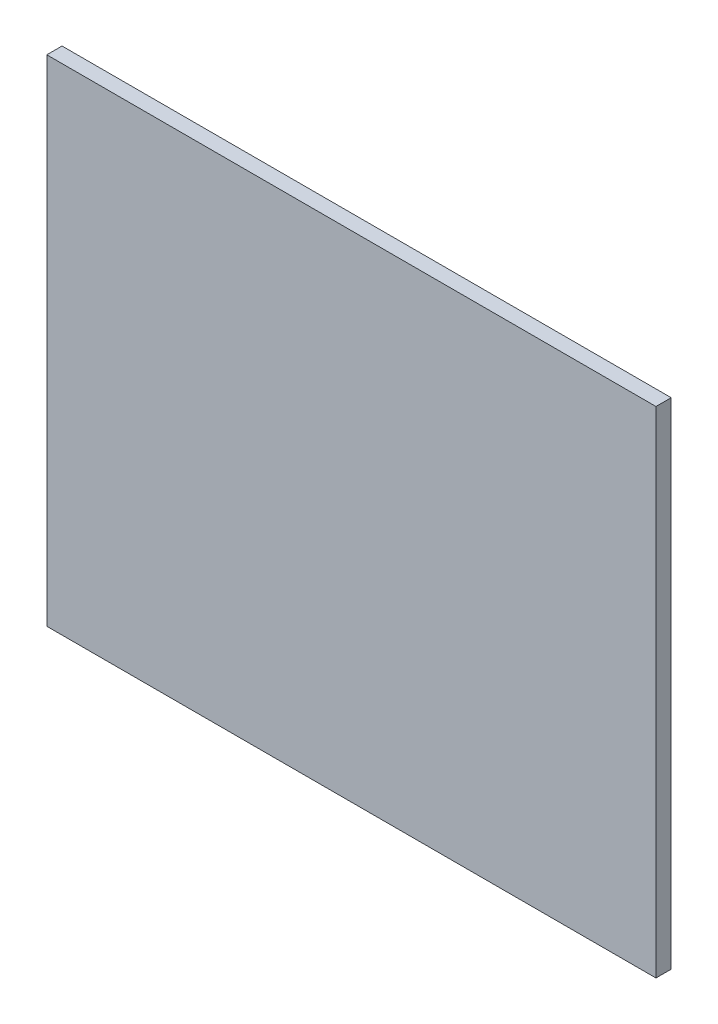
SolidWorks part; units mm, degrees
ref_plane "前视基准面" through (0, 0, 0) normal (0, 0, 1) x (1, 0, 0)
ref_plane "上视基准面" through (0, 0, 0) normal (0, 1, 0) x (1, 0, 0)
ref_plane "右视基准面" through (0, 0, 0) normal (1, 0, 0) x (0, 0, -1)
sketch "草图1" plane through (0, 0, 0) normal (0, 0, 1) x (1, 0, 0)
  line L1 (-400, -325) -> (400, -325)
  line L2 (-400, -325) -> (-400, 325)
  line L3 (-400, 325) -> (400, 325)
  line L4 (400, -325) -> (400, 325)
  line L5 (-400, -325) -> (400, 325) construction
  line L6 (-400, 325) -> (400, -325) construction
  point P0 (0, 0)
  dimension "D1" = 650
  dimension "D2" = 800
extrude "凸台-拉伸1" add sketch "草图1" along normal blind 20
